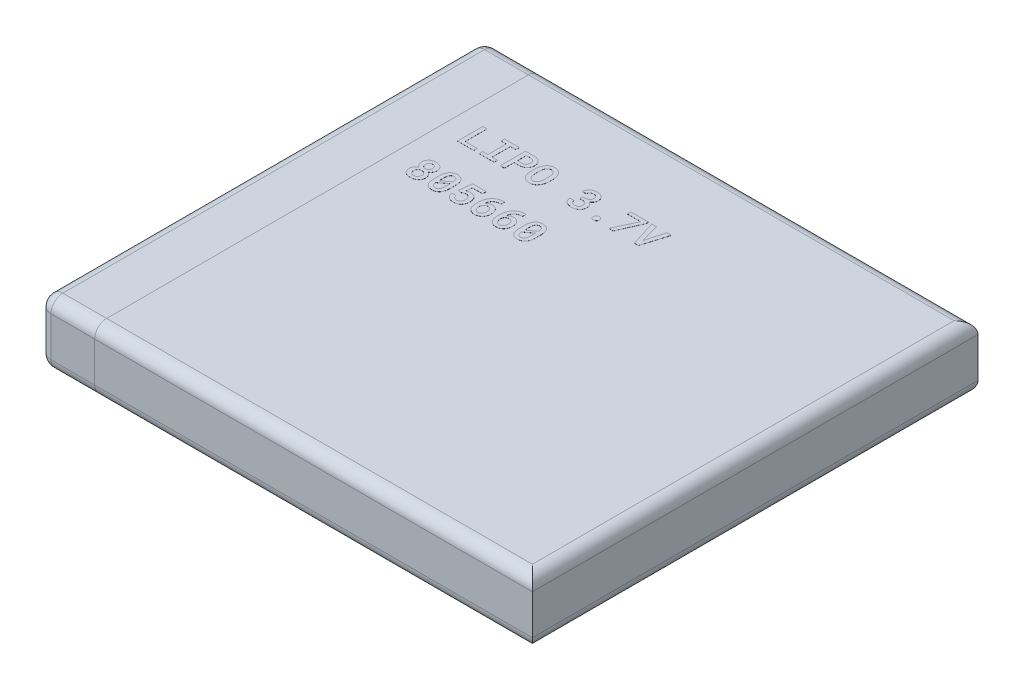
SolidWorks part; units mm, degrees
ref_plane "Front Plane" through (0, 0, 0) normal (0, 0, 1) x (1, 0, 0)
ref_plane "Top Plane" through (0, 0, 0) normal (0, 1, 0) x (1, 0, 0)
ref_plane "Right Plane" through (0, 0, 0) normal (1, 0, 0) x (0, 0, -1)
sketch "Sketch1" plane through (0, 0, 0) normal (0, 1, 0) x (1, 0, 0)
  line L1 (-19.6052, -46.8717) -> (35.3948, -46.8717)
  line L2 (-19.6052, -46.8717) -> (-19.6052, 9.1283)
  line L3 (-19.6052, 9.1283) -> (35.3948, 9.1283)
  line L4 (35.3948, -46.8717) -> (35.3948, 9.1283)
  dimension "D1" = 55
  dimension "D2" = 56
extrude "Boss-Extrude1" add sketch "Sketch1" along normal blind 8
sketch "Sketch2" plane through (-19.6052, 0, 0) normal (-1, 0, 0) x (0, 0, 1)
  line L1 (-9.1283, 8) -> (46.8717, 8)
  line L2 (-9.1283, 8) -> (-9.1283, 0)
  line L3 (-9.1283, 0) -> (46.8717, 0)
  line L4 (46.8717, 8) -> (46.8717, 0)
extrude "Boss-Extrude3" add sketch "Sketch2" along normal blind 7 separate body
fillet "Fillet1" radius 1.5 6 edges at (35.3948, 8, 18.8717) (35.3948, 0, 18.8717) (7.8948, 0, 46.8717) (7.8948, 0, -9.1283) (7.8948, 8, -9.1283) (7.8948, 8, 46.8717)
fillet "Fillet2" radius 1.5 8 edges at (-26.6052, 4, 46.8717) (-23.1052, 8, 46.8717) (-23.1052, 0, 46.8717) (-23.1052, 0, -9.1283) (-26.6052, 0, 18.8717) (-26.6052, 8, 18.8717) (-26.6052, 4, -9.1283) (-23.1052, 8, -9.1283)
sketch "Sketch3" plane through (0, 8, 0) normal (0, 1, 0) x (1, 0, 0)
  text T0 "<b>LIPO 3.7V</b>\r\n<b>805660</b>" font "Roboto Mono Medium" height 3.175
extrude "Boss-Extrude5" add sketch "Sketch3" along normal blind 0.01 separate body
